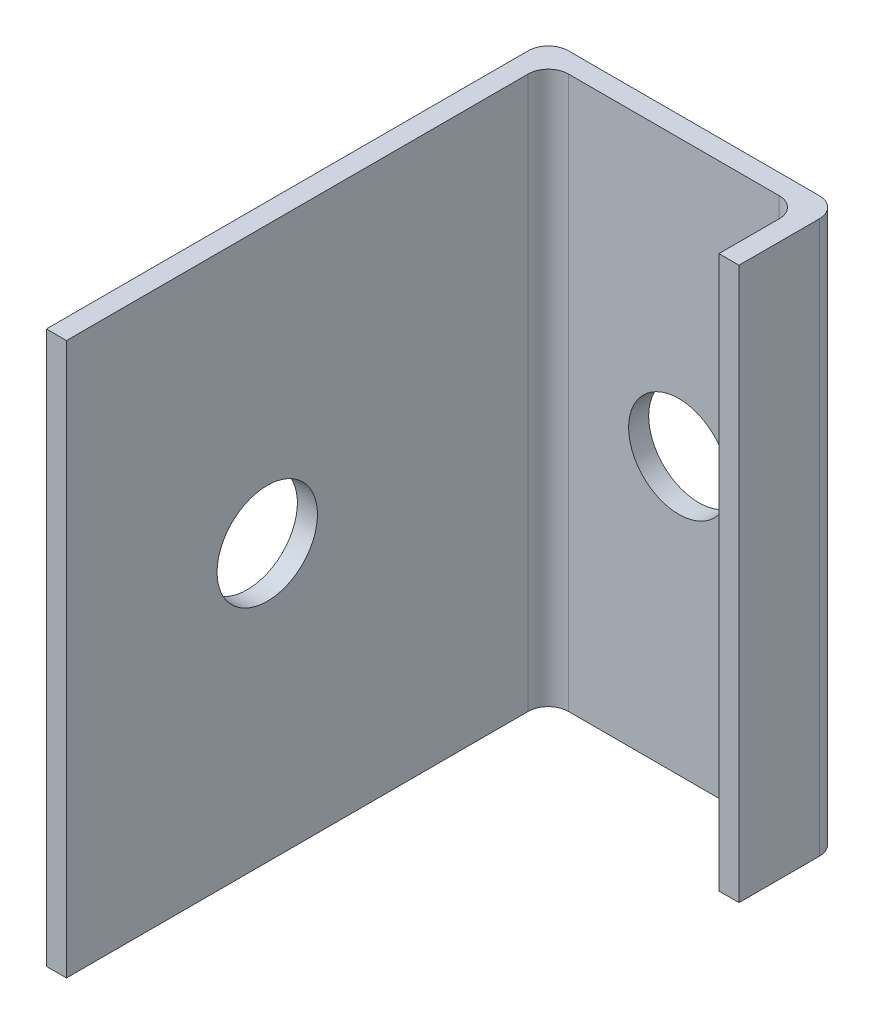
SolidWorks part; units mm, degrees
ref_plane "Front Plane" through (0, 0, 0) normal (0, 0, 1) x (1, 0, 0)
ref_plane "Top Plane" through (0, 0, 0) normal (0, 1, 0) x (1, 0, 0)
ref_plane "Right Plane" through (0, 0, 0) normal (1, 0, 0) x (0, 0, -1)
sketch "Sketch1" plane through (0, 0, 0) normal (0, 1, 0) x (1, 0, 0)
  line L0 (-61.1614, -27.4878) -> (-61.1614, 20.5122)
  line L1 (-59.1614, 22.5122) -> (-34.1614, 22.5122)
  line L2 (-32.1614, 20.5122) -> (-32.1614, 12.5122)
  line L3 (-61.1614, -27.4878) -> (-59.1614, -27.4878)
  line L4 (-59.1614, -27.4878) -> (-59.1614, 18.5122)
  line L5 (-57.1614, 20.5122) -> (-36.1614, 20.5122)
  line L6 (-34.1614, 18.5122) -> (-34.1614, 12.5122)
  line L7 (-34.1614, 12.5122) -> (-32.1614, 12.5122)
  arc A0 (-57.1614, 20.5122) -> (-59.1614, 18.5122) centre (-57.1614, 18.5122) ccw
  arc A1 (-36.1614, 20.5122) -> (-34.1614, 18.5122) centre (-36.1614, 18.5122) cw
  arc A2 (-32.1614, 20.5122) -> (-34.1614, 22.5122) centre (-34.1614, 20.5122) ccw
  arc A3 (-59.1614, 22.5122) -> (-61.1614, 20.5122) centre (-59.1614, 20.5122) ccw
  point P12 (-34.1614, 20.5122)
  point P15 (-32.1614, 22.5122)
  point P18 (-61.1614, 22.5122)
  dimension "D7" = 2
  dimension "D1" = 50
  dimension "D2" = 29
  dimension "D3" = 10
  dimension "D4" = 2
  dimension "D5" = 2
  dimension "D6" = 2
extrude "Boss-Extrude1" add sketch "Sketch1" along normal blind 55
ref_plane "Plane1" through (0, 0, -22.5122) normal (0, 0, -1) x (-1, 0, 0)
sketch "Sketch2" plane through (0, 0, -22.5122) normal (0, 0, -1) x (-1, 0, 0)
  line L1 (32.1614, 55) -> (61.1614, 55)
  line L2 (32.1614, 55) -> (32.1614, 0)
  line L3 (32.1614, 0) -> (61.1614, 0)
  line L4 (61.1614, 55) -> (61.1614, 0)
  point P0 (46.1614, 27.5)
  dimension "D1" = 15
  dimension "D2" = 27.5
hole_wizard "M10x1.0 Tapped Hole2" positions "3DSketch1" profile "Sketch3" tap size "M10x1.0" standard "ANSI Metric"
sketch3d "3DSketch1"
  point P0 (-46.1614, 27.5, -22.5122)
sketch "Sketch3" plane through (-46.1614, 27.5, -22.5122) normal (1, 0, 0) x (0, 1, 0)
  line L0 (0, 0) -> (0, 25.7039)
  line L1 (0, 25.7039) -> (4.5, 23)
  line L2 (4.5, 23) -> (4.5, 20)
  line L3 (4.5, 20) -> (5, 20)
  line L4 (5, 20) -> (5, 0)
  line L5 (5, 0) -> (0, 0)
  line L10 (0, 25.7039) -> (-4.5, 23) construction
  line L11 (0, -6.35) -> (0, 107.95) construction
  dimension "Tap Drill Dia." = 9
  dimension "Tap Drill Depth" = 23
  dimension "Thread Major Dia." = 10
  dimension "Thread Depth" = 20
  dimension "Drill Angle" = 118
ref_plane "Plane2" through (-61.1614, 0, 0) normal (-1, 0, 0) x (0, 0, 1)
sketch "Sketch4" plane through (-61.1614, 0, 0) normal (-1, 0, 0) x (0, 0, 1)
  line L0 (27.4878, 55) -> (27.4878, 0) construction
  line L1 (-20.5122, 0) -> (27.4878, 0) construction
  point P0 (7.4878, 27.5)
  dimension "D1" = 20
  dimension "D2" = 27.5
hole_wizard "M10x1.0 Tapped Hole1" positions "3DSketch2" profile "Sketch5" tap size "M10x1.0" standard "ANSI Metric"
sketch3d "3DSketch2"
  point P0 (-61.1614, 27.5, 7.4878)
sketch "Sketch5" plane through (-61.1614, 27.5, 7.4878) normal (0, 1, 0) x (0, 0, 1)
  line L0 (0, 0) -> (0, 25.7039)
  line L1 (0, 25.7039) -> (4.5, 23)
  line L2 (4.5, 23) -> (4.5, 20)
  line L3 (4.5, 20) -> (5, 20)
  line L4 (5, 20) -> (5, 0)
  line L5 (5, 0) -> (0, 0)
  line L10 (0, 25.7039) -> (-4.5, 23) construction
  line L11 (0, -6.35) -> (0, 107.95) construction
  dimension "Tap Drill Dia." = 9
  dimension "Tap Drill Depth" = 23
  dimension "Thread Major Dia." = 10
  dimension "Thread Depth" = 20
  dimension "Drill Angle" = 118
